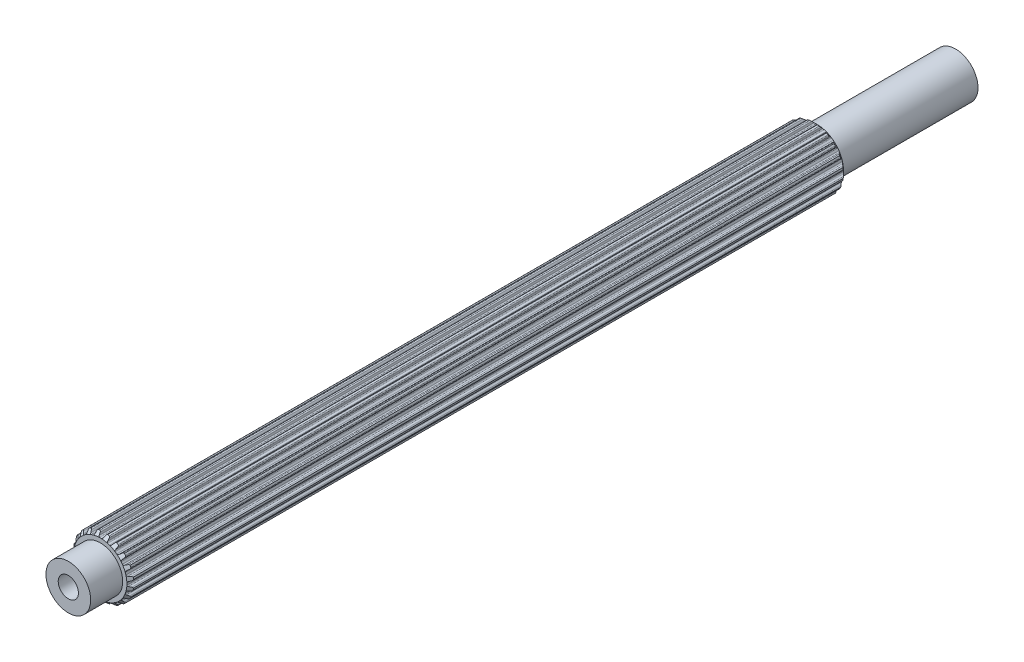
SolidWorks part; units mm, degrees
ref_plane "Front Plane" through (0, 0, 0) normal (0, 0, 1) x (1, 0, 0)
ref_plane "Top Plane" through (0, 0, 0) normal (0, 1, 0) x (1, 0, 0)
ref_plane "Right Plane" through (0, 0, 0) normal (1, 0, 0) x (0, 0, -1)
sketch "Sketch1" plane through (0, 0, 0) normal (0, 0, 1) x (1, 0, 0)
  line L0 (-0.1069, 2.9699) -> (0.1069, 2.9699)
  line L1 (0.3159, 3.2375) -> (0.2537, 3.0575)
  line L2 (-0.2964, 3.2367) -> (-0.2318, 3.0575)
  line L3 (-0.2964, 3.2367) -> (0.3159, 3.2375) construction
  line L4 (0, 3.3252) -> (0, 0) construction
  line L5 (-0.2318, 3.0575) -> (0.2537, 3.0575) construction
  line L6 (-0.4281, 3.3241) -> (0.4281, 3.3263) construction
  line L7 (0.7183, 3.1698) -> (0.7244, 2.9795)
  line L8 (0.816, 2.8576) -> (1.0195, 2.7915)
  line L9 (1.3009, 2.9815) -> (1.1862, 2.8295)
  line L10 (1.6627, 2.7927) -> (1.6097, 2.6099)
  line L11 (1.6591, 2.4655) -> (1.8322, 2.3398)
  line L12 (2.1585, 2.4335) -> (2.0025, 2.3245)
  line L13 (2.4443, 2.1423) -> (2.3374, 1.9847)
  line L14 (2.3398, 1.8322) -> (2.4655, 1.6591)
  line L15 (2.8049, 1.6474) -> (2.6228, 1.5919)
  line L16 (2.9866, 1.2821) -> (2.8363, 1.1653)
  line L17 (2.7915, 1.0195) -> (2.8576, 0.816)
  line L18 (3.1767, 0.7) -> (2.9863, 0.7035)
  line L19 (3.2367, 0.2964) -> (3.0575, 0.2318)
  line L20 (2.9699, 0.1069) -> (2.9699, -0.1069)
  line L21 (3.2375, -0.3159) -> (3.0575, -0.2537)
  line L22 (3.1698, -0.7183) -> (2.9795, -0.7244)
  line L23 (2.8576, -0.816) -> (2.7915, -1.0195)
  line L24 (2.9815, -1.3009) -> (2.8295, -1.1862)
  line L25 (2.7927, -1.6627) -> (2.6099, -1.6097)
  line L26 (2.4655, -1.6591) -> (2.3398, -1.8322)
  line L27 (2.4335, -2.1585) -> (2.3245, -2.0025)
  line L28 (2.1423, -2.4443) -> (1.9847, -2.3374)
  line L29 (1.8322, -2.3398) -> (1.6591, -2.4655)
  line L30 (1.6474, -2.8049) -> (1.5919, -2.6228)
  line L31 (1.2821, -2.9866) -> (1.1653, -2.8363)
  line L32 (1.0195, -2.7915) -> (0.816, -2.8576)
  line L33 (0.7, -3.1767) -> (0.7035, -2.9863)
  line L34 (0.2964, -3.2367) -> (0.2318, -3.0575)
  line L35 (0.1069, -2.9699) -> (-0.1069, -2.9699)
  line L36 (-0.3159, -3.2375) -> (-0.2537, -3.0575)
  line L37 (-0.7183, -3.1698) -> (-0.7244, -2.9795)
  line L38 (-0.816, -2.8576) -> (-1.0195, -2.7915)
  line L39 (-1.3009, -2.9815) -> (-1.1862, -2.8295)
  line L40 (-1.6627, -2.7927) -> (-1.6097, -2.6099)
  line L41 (-1.6591, -2.4655) -> (-1.8322, -2.3398)
  line L42 (-2.1585, -2.4335) -> (-2.0025, -2.3245)
  line L43 (-2.4443, -2.1423) -> (-2.3374, -1.9847)
  line L44 (-2.3398, -1.8322) -> (-2.4655, -1.6591)
  line L45 (-2.8049, -1.6474) -> (-2.6228, -1.5919)
  line L46 (-2.9866, -1.2821) -> (-2.8363, -1.1653)
  line L47 (-2.7915, -1.0195) -> (-2.8576, -0.816)
  line L48 (-3.1767, -0.7) -> (-2.9863, -0.7035)
  line L49 (-3.2367, -0.2964) -> (-3.0575, -0.2318)
  line L50 (-2.9699, -0.1069) -> (-2.9699, 0.1069)
  line L51 (-3.2375, 0.3159) -> (-3.0575, 0.2537)
  line L52 (-3.1698, 0.7183) -> (-2.9795, 0.7244)
  line L53 (-2.8576, 0.816) -> (-2.7915, 1.0195)
  line L54 (-2.9815, 1.3009) -> (-2.8295, 1.1862)
  line L55 (-2.7927, 1.6627) -> (-2.6099, 1.6097)
  line L56 (-2.4655, 1.6591) -> (-2.3398, 1.8322)
  line L57 (-2.4335, 2.1585) -> (-2.3245, 2.0025)
  line L58 (-2.1423, 2.4443) -> (-1.9847, 2.3374)
  line L59 (-1.8322, 2.3398) -> (-1.6591, 2.4655)
  line L60 (-1.6474, 2.8049) -> (-1.5919, 2.6228)
  line L61 (-1.2821, 2.9866) -> (-1.1653, 2.8363)
  line L62 (-1.0195, 2.7915) -> (-0.816, 2.8576)
  line L63 (-0.7, 3.1767) -> (-0.7035, 2.9863)
  line L64 (0.4281, 3.3263) -> (0.62, 3.2938)
  line L65 (1.4351, 3.0312) -> (1.6075, 2.9409)
  line L66 (2.3015, 2.4394) -> (2.4376, 2.3003)
  line L67 (2.9427, 1.6088) -> (3.0291, 1.4344)
  line L68 (3.2958, 0.6207) -> (3.3241, 0.4281)
  line L69 (3.3263, -0.4281) -> (3.2938, -0.62)
  line L70 (3.0312, -1.4351) -> (2.9409, -1.6075)
  line L71 (2.4394, -2.3015) -> (2.3003, -2.4376)
  line L72 (1.6088, -2.9427) -> (1.4344, -3.0291)
  line L73 (0.6207, -3.2958) -> (0.4281, -3.3241)
  line L74 (-0.4281, -3.3263) -> (-0.62, -3.2938)
  line L75 (-1.4351, -3.0312) -> (-1.6075, -2.9409)
  line L76 (-2.3015, -2.4394) -> (-2.4376, -2.3003)
  line L77 (-2.9427, -1.6088) -> (-3.0291, -1.4344)
  line L78 (-3.2958, -0.6207) -> (-3.3241, -0.4281)
  line L79 (-3.3263, 0.4281) -> (-3.2938, 0.62)
  line L80 (-3.0312, 1.4351) -> (-2.9409, 1.6075)
  line L81 (-2.4394, 2.3015) -> (-2.3003, 2.4376)
  line L82 (-1.6088, 2.9427) -> (-1.4344, 3.0291)
  line L83 (-0.6207, 3.2958) -> (-0.4281, 3.3241)
  arc A0 (0.2537, 3.0575) -> (0.1069, 2.9699) centre (0.1283, 3.1009) cw
  arc A1 (-0.2318, 3.0575) -> (-0.1069, 2.9699) centre (-0.1069, 3.1026) ccw
  arc A2 (0.62, 3.2938) -> (0.7183, 3.1698) centre (0.5856, 3.1656) cw
  arc A3 (0.7244, 2.9795) -> (0.816, 2.8576) centre (0.857, 2.9838) ccw
  arc A4 (-0.4281, 3.3241) -> (-0.2964, 3.2367) centre (-0.4213, 3.1916) cw
  arc A5 (0.4281, 3.3263) -> (0.3159, 3.2375) centre (0.4413, 3.1942) ccw
  arc A6 (1.1862, 2.8295) -> (1.0195, 2.7915) centre (1.0802, 2.9095) cw
  arc A7 (1.4351, 3.0312) -> (1.3009, 2.9815) centre (1.4068, 2.9015) ccw
  arc A8 (1.6075, 2.9409) -> (1.6627, 2.7927) centre (1.5352, 2.8297) cw
  arc A9 (1.6097, 2.6099) -> (1.6591, 2.4655) centre (1.7371, 2.5729) ccw
  arc A10 (2.0025, 2.3245) -> (1.8322, 2.3398) centre (1.9264, 2.4332) cw
  arc A11 (2.3015, 2.4394) -> (2.1585, 2.4335) centre (2.2346, 2.3248) ccw
  arc A12 (2.4376, 2.3003) -> (2.4443, 2.1423) centre (2.3345, 2.2168) cw
  arc A13 (2.3374, 1.9847) -> (2.3398, 1.8322) centre (2.4472, 1.9102) ccw
  arc A14 (2.6228, 1.5919) -> (2.4655, 1.6591) centre (2.5841, 1.7189) cw
  arc A15 (2.9427, 1.6088) -> (2.8049, 1.6474) centre (2.8436, 1.5205) ccw
  arc A16 (3.0291, 1.4344) -> (2.9866, 1.2821) centre (2.9052, 1.3869) cw
  arc A17 (2.8363, 1.1653) -> (2.7915, 1.0195) centre (2.9177, 1.0605) ccw
  arc A18 (2.9863, 0.7035) -> (2.8576, 0.816) centre (2.9887, 0.8362) cw
  arc A19 (3.2958, 0.6207) -> (3.1767, 0.7) centre (3.1743, 0.5673) ccw
  arc A20 (3.3241, 0.4281) -> (3.2367, 0.2964) centre (3.1916, 0.4213) cw
  arc A21 (3.0575, 0.2318) -> (2.9699, 0.1069) centre (3.1026, 0.1069) ccw
  arc A22 (3.0575, -0.2537) -> (2.9699, -0.1069) centre (3.1009, -0.1283) cw
  arc A23 (3.3263, -0.4281) -> (3.2375, -0.3159) centre (3.1942, -0.4413) ccw
  arc A24 (3.2938, -0.62) -> (3.1698, -0.7183) centre (3.1656, -0.5856) cw
  arc A25 (2.9795, -0.7244) -> (2.8576, -0.816) centre (2.9838, -0.857) ccw
  arc A26 (2.8295, -1.1862) -> (2.7915, -1.0195) centre (2.9095, -1.0802) cw
  arc A27 (3.0312, -1.4351) -> (2.9815, -1.3009) centre (2.9015, -1.4068) ccw
  arc A28 (2.9409, -1.6075) -> (2.7927, -1.6627) centre (2.8297, -1.5352) cw
  arc A29 (2.6099, -1.6097) -> (2.4655, -1.6591) centre (2.5729, -1.7371) ccw
  arc A30 (2.3245, -2.0025) -> (2.3398, -1.8322) centre (2.4332, -1.9264) cw
  arc A31 (2.4394, -2.3015) -> (2.4335, -2.1585) centre (2.3248, -2.2346) ccw
  arc A32 (2.3003, -2.4376) -> (2.1423, -2.4443) centre (2.2168, -2.3345) cw
  arc A33 (1.9847, -2.3374) -> (1.8322, -2.3398) centre (1.9102, -2.4472) ccw
  arc A34 (1.5919, -2.6228) -> (1.6591, -2.4655) centre (1.7189, -2.5841) cw
  arc A35 (1.6088, -2.9427) -> (1.6474, -2.8049) centre (1.5205, -2.8436) ccw
  arc A36 (1.4344, -3.0291) -> (1.2821, -2.9866) centre (1.3869, -2.9052) cw
  arc A37 (1.1653, -2.8363) -> (1.0195, -2.7915) centre (1.0605, -2.9177) ccw
  arc A38 (0.7035, -2.9863) -> (0.816, -2.8576) centre (0.8362, -2.9887) cw
  arc A39 (0.6207, -3.2958) -> (0.7, -3.1767) centre (0.5673, -3.1743) ccw
  arc A40 (0.4281, -3.3241) -> (0.2964, -3.2367) centre (0.4213, -3.1916) cw
  arc A41 (0.2318, -3.0575) -> (0.1069, -2.9699) centre (0.1069, -3.1026) ccw
  arc A42 (-0.2537, -3.0575) -> (-0.1069, -2.9699) centre (-0.1283, -3.1009) cw
  arc A43 (-0.4281, -3.3263) -> (-0.3159, -3.2375) centre (-0.4413, -3.1942) ccw
  arc A44 (-0.62, -3.2938) -> (-0.7183, -3.1698) centre (-0.5856, -3.1656) cw
  arc A45 (-0.7244, -2.9795) -> (-0.816, -2.8576) centre (-0.857, -2.9838) ccw
  arc A46 (-1.1862, -2.8295) -> (-1.0195, -2.7915) centre (-1.0802, -2.9095) cw
  arc A47 (-1.4351, -3.0312) -> (-1.3009, -2.9815) centre (-1.4068, -2.9015) ccw
  arc A48 (-1.6075, -2.9409) -> (-1.6627, -2.7927) centre (-1.5352, -2.8297) cw
  arc A49 (-1.6097, -2.6099) -> (-1.6591, -2.4655) centre (-1.7371, -2.5729) ccw
  arc A50 (-2.0025, -2.3245) -> (-1.8322, -2.3398) centre (-1.9264, -2.4332) cw
  arc A51 (-2.3015, -2.4394) -> (-2.1585, -2.4335) centre (-2.2346, -2.3248) ccw
  arc A52 (-2.4376, -2.3003) -> (-2.4443, -2.1423) centre (-2.3345, -2.2168) cw
  arc A53 (-2.3374, -1.9847) -> (-2.3398, -1.8322) centre (-2.4472, -1.9102) ccw
  arc A54 (-2.6228, -1.5919) -> (-2.4655, -1.6591) centre (-2.5841, -1.7189) cw
  arc A55 (-2.9427, -1.6088) -> (-2.8049, -1.6474) centre (-2.8436, -1.5205) ccw
  arc A56 (-3.0291, -1.4344) -> (-2.9866, -1.2821) centre (-2.9052, -1.3869) cw
  arc A57 (-2.8363, -1.1653) -> (-2.7915, -1.0195) centre (-2.9177, -1.0605) ccw
  arc A58 (-2.9863, -0.7035) -> (-2.8576, -0.816) centre (-2.9887, -0.8362) cw
  arc A59 (-3.2958, -0.6207) -> (-3.1767, -0.7) centre (-3.1743, -0.5673) ccw
  arc A60 (-3.3241, -0.4281) -> (-3.2367, -0.2964) centre (-3.1916, -0.4213) cw
  arc A61 (-3.0575, -0.2318) -> (-2.9699, -0.1069) centre (-3.1026, -0.1069) ccw
  arc A62 (-3.0575, 0.2537) -> (-2.9699, 0.1069) centre (-3.1009, 0.1283) cw
  arc A63 (-3.3263, 0.4281) -> (-3.2375, 0.3159) centre (-3.1942, 0.4413) ccw
  arc A64 (-3.2938, 0.62) -> (-3.1698, 0.7183) centre (-3.1656, 0.5856) cw
  arc A65 (-2.9795, 0.7244) -> (-2.8576, 0.816) centre (-2.9838, 0.857) ccw
  arc A66 (-2.8295, 1.1862) -> (-2.7915, 1.0195) centre (-2.9095, 1.0802) cw
  arc A67 (-3.0312, 1.4351) -> (-2.9815, 1.3009) centre (-2.9015, 1.4068) ccw
  arc A68 (-2.9409, 1.6075) -> (-2.7927, 1.6627) centre (-2.8297, 1.5352) cw
  arc A69 (-2.6099, 1.6097) -> (-2.4655, 1.6591) centre (-2.5729, 1.7371) ccw
  arc A70 (-2.3245, 2.0025) -> (-2.3398, 1.8322) centre (-2.4332, 1.9264) cw
  arc A71 (-2.4394, 2.3015) -> (-2.4335, 2.1585) centre (-2.3248, 2.2346) ccw
  arc A72 (-2.3003, 2.4376) -> (-2.1423, 2.4443) centre (-2.2168, 2.3345) cw
  arc A73 (-1.9847, 2.3374) -> (-1.8322, 2.3398) centre (-1.9102, 2.4472) ccw
  arc A74 (-1.5919, 2.6228) -> (-1.6591, 2.4655) centre (-1.7189, 2.5841) cw
  arc A75 (-1.6088, 2.9427) -> (-1.6474, 2.8049) centre (-1.5205, 2.8436) ccw
  arc A76 (-1.4344, 3.0291) -> (-1.2821, 2.9866) centre (-1.3869, 2.9052) cw
  arc A77 (-1.1653, 2.8363) -> (-1.0195, 2.7915) centre (-1.0605, 2.9177) ccw
  arc A78 (-0.7035, 2.9863) -> (-0.816, 2.8576) centre (-0.8362, 2.9887) cw
  arc A79 (-0.6207, 3.2958) -> (-0.7, 3.1767) centre (-0.5673, 3.1743) ccw
  point P14 (0, 2.9699)
  point P247 (0, 0)
  dimension "D4" = 0.1327
  dimension "D8" = 20
  dimension "D1" = 2.9699
  dimension "D2" = 0.2139
  dimension "D3" = 0.1904
  dimension "D5" = 0.0877
  dimension "D6" = 0.4855
  dimension "D7" = 0.8563
extrude "Boss-Extrude1" add sketch "Sketch1" along normal blind 46.0477 and the other way blind 34.1097
sketch "Sketch2" plane through (0, 0, 0) normal (0, 0, 1) x (1, 0, 0)
  circle A0 centre (0, 0) radius 2.5019
  dimension "D1" = 5.0038
extrude "Boss-Extrude2" add sketch "Sketch2" along normal mid plane 99.2581
sketch "Sketch4" plane through (0, 0, 49.6291) normal (0, 0, 1) x (1, 0, 0)
  circle A0 centre (0, 0) radius 2.5019 construction
  point P0 (0, 0)
sketch "Sketch5" plane through (0, 0, -49.6291) normal (0, 0, -1) x (-1, 0, 0)
  circle A0 centre (0, 0) radius 2.5019 construction
  point P0 (0, 0)
sketch "Sketch3" plane through (0, 0, 0) normal (1, 0, 0) x (0, 0, -1)
  line L0 (-44.9164, 4.1011) -> (-46.0477, 2.9699)
  line L1 (-46.0477, 2.9699) -> (-46.0477, 4.1011)
  line L2 (-46.0477, 4.1011) -> (-44.9164, 4.1011)
  line L3 (-46.0477, 2.5019) -> (-46.0477, -2.5019) construction
  line L5 (-14.3608, 0) -> (13.2171, 0) construction
  line L7 (34.1097, 30.8235) -> (34.1097, 2.9699)
  line L8 (34.1097, 2.9699) -> (20.1828, 16.8967)
  line L9 (20.1828, 16.8967) -> (34.1097, 30.8235)
  line L10 (34.1097, -2.5019) -> (34.1097, 2.5019) construction
  point P6 (-4.866, 6.1438)
  dimension "D1" = 45
  dimension "D2" = 45
revolve "Cut-Revolve1" cut sketch "Sketch3" angle 360 about L5
sketch "Sketch6" plane through (0, 0, 0) normal (0, 1, 0) x (1, 0, 0)
  line L0 (-15.5223, 0) -> (15.5223, 0) construction
sketch "Sketch7" plane through (0, 0, 0) normal (0, 0, 1) x (1, 0, 0)
  circle A0 centre (0, 0) radius 1.1303
  point P2 (3.1007, -1.5407)
  dimension "D1" = 2.2606
extrude "Cut-Extrude1" cut sketch "Sketch7" against normal up to surface and the other way up to surface up to face at (2.5019, 0, -49.6291) other way up to face at (2.5019, 0, 49.6291)
sketch "Sketch8" plane through (0, 0, 0) normal (0, 0, 1) x (1, 0, 0)
  circle A0 centre (0, 0) radius 1.1303
  circle A1 centre (0, 0) radius 1.1303 construction
  point P2 (4.9455, -5.8362)
extrude "Boss-Extrude3" add sketch "Sketch8" along normal offset from surface 9.525 and the other way offset from surface (40.1041 mm away) 9.525 up to face at (1.1303, 0, 49.6291) other way up to face at (1.1303, 0, -49.6291)
